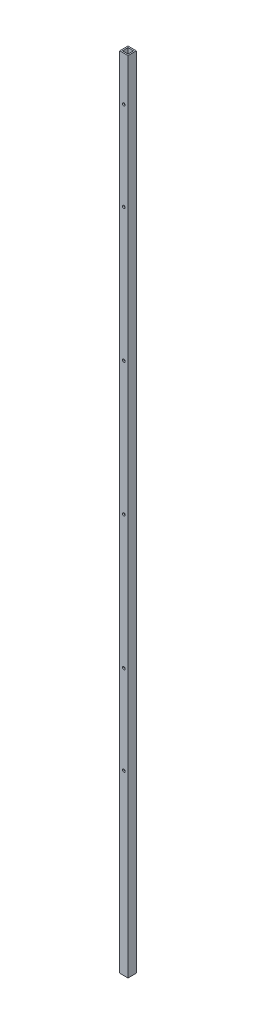
SolidWorks part; units mm, degrees
material "1023 Carbon Steel Sheet (SS)"
ref_plane "Front Plane" through (0, 0, 0) normal (0, 0, 1) x (1, 0, 0)
ref_plane "Top Plane" through (0, 0, 0) normal (0, 1, 0) x (1, 0, 0)
ref_plane "Right Plane" through (0, 0, 0) normal (1, 0, 0) x (0, 0, -1)
sketch "Sketch1" plane through (0, 0, 0) normal (0, 1, 0) x (1, 0, 0)
  line L1 (0, 0) -> (19.05, 0)
  line L2 (0, 0) -> (0, 19.05)
  line L3 (0, 19.05) -> (19.05, 19.05)
  line L4 (19.05, 0) -> (19.05, 19.05)
  dimension "D1" = 19.05
  dimension "D2" = 19.05
extrude "Boss-Extrude1" add sketch "Sketch1" along normal blind 1828.8
sketch "Sketch2" plane through (0, 1828.8, 0) normal (0, 1, 0) x (1, 0, 0)
  line L0 (0, 19.05) -> (0, 0) construction
  line L1 (3.175, 3.175) -> (15.875, 3.175)
  line L2 (3.175, 3.175) -> (3.175, 15.875)
  line L3 (3.175, 15.875) -> (15.875, 15.875)
  line L4 (15.875, 3.175) -> (15.875, 15.875)
  line L5 (0, 0) -> (19.05, 0) construction
  dimension "D1" = 12.7
  dimension "D2" = 12.7
  dimension "D3" = 3.175
  dimension "D4" = 3.175
extrude "Cut-Extrude1" cut sketch "Sketch2" against normal through all
sketch "Sketch3" plane through (0, 0, 0) normal (0, 0, 1) x (1, 0, 0)
  line L0 (0, 1828.8) -> (0, 0) construction
  line L1 (0, 1828.8) -> (19.05, 1828.8) construction
  line L2 (0, 0) -> (19.05, 0) construction
  circle A0 centre (9.525, 1727.2) radius 3.175
  circle A1 centre (9.525, 1524) radius 3.175
  circle A2 centre (9.525, 1219.2) radius 3.175
  circle A3 centre (9.525, 914.4) radius 3.175
  circle A4 centre (9.525, 406.4) radius 3.175
  circle A5 centre (9.525, 609.6) radius 3.175
  dimension "D1" = 6.35
  dimension "D4" = 6.35
  dimension "D5" = 304.8
  dimension "D6" = 6.35
  dimension "D7" = 609.6
  dimension "D8" = 6.35
  dimension "D10" = 6.35
  dimension "D12" = 6.35
  dimension "D2" = 9.525
  dimension "D3" = 101.6
  dimension "D9" = 914.4
  dimension "D11" = 406.4
  dimension "D13" = 609.6
extrude "Cut-Extrude2" cut sketch "Sketch3" against normal through all
